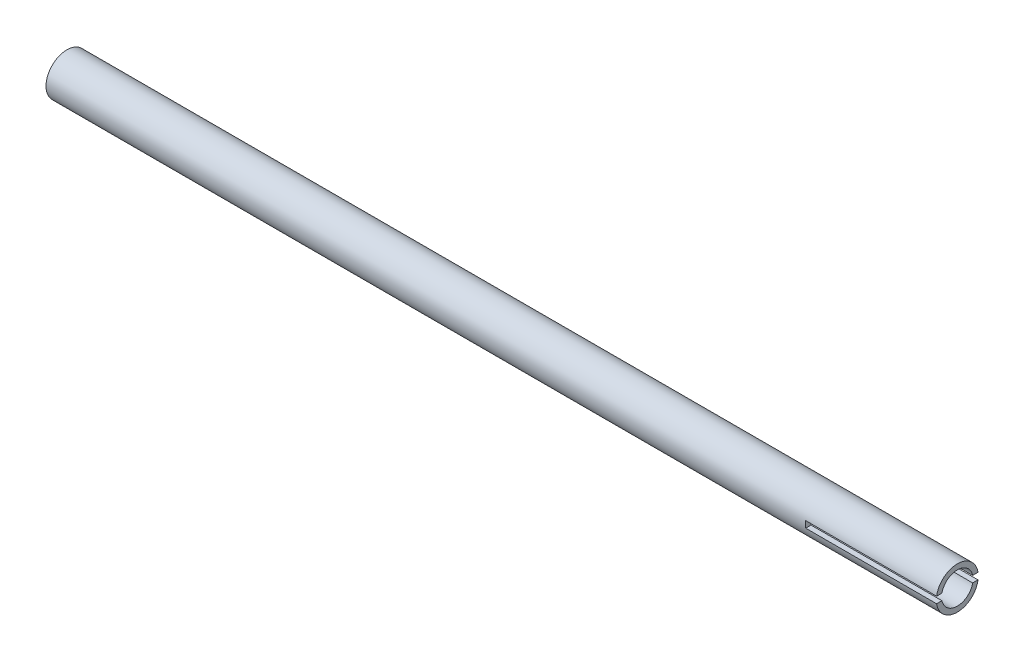
SolidWorks part; units mm, degrees
ref_plane "Front Plane" through (0, 0, 0) normal (0, 0, 1) x (1, 0, 0)
ref_plane "Top Plane" through (0, 0, 0) normal (0, 1, 0) x (1, 0, 0)
ref_plane "Right Plane" through (0, 0, 0) normal (1, 0, 0) x (0, 0, -1)
sketch "Sketch1" plane through (0, 0, 0) normal (1, 0, 0) x (0, 0, -1)
  circle A0 centre (0, 0) radius 8
  circle A1 centre (0, 0) radius 6
  dimension "D1" = 16
  dimension "D2" = 2
extrude "Boss-Extrude1" add sketch "Sketch1" along normal mid plane 340
sketch "Sketch2" plane through (0, 0, 0) normal (0, 0, 1) x (1, 0, 0)
  line L0 (170, -8) -> (170, 8) construction
  line L1 (170, 1.25) -> (120, 1.25)
  line L2 (170, 1.25) -> (170, -1.25)
  line L3 (170, -1.25) -> (120, -1.25)
  line L4 (120, 1.25) -> (120, -1.25)
  line L5 (170, 0) -> (0, 0) construction
  point P9 (0, 0)
  dimension "D1" = 2.5
  dimension "D2" = 50
extrude "Cut-Extrude1" cut sketch "Sketch2" against normal through all both and the other way through all
